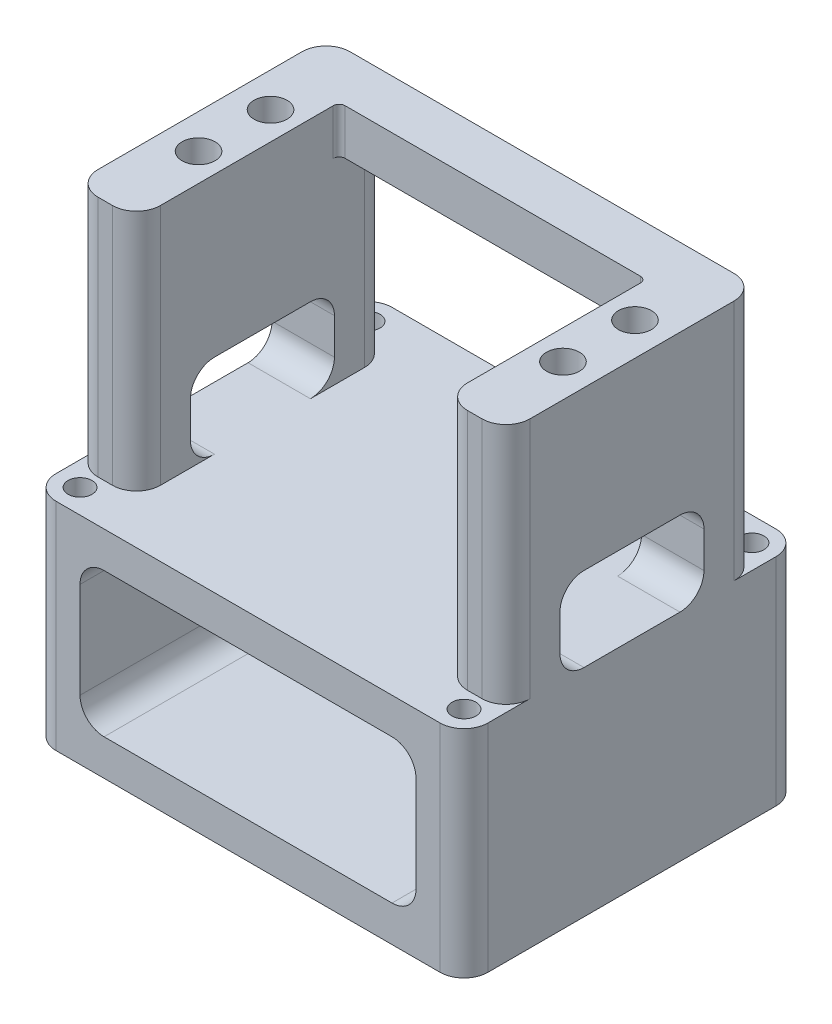
SolidWorks part; units mm, degrees
ref_plane "Front" through (0, 0, 0) normal (0, 0, 1) x (1, 0, 0)
ref_plane "Top" through (0, 0, 0) normal (0, 1, 0) x (1, 0, 0)
ref_plane "Right" through (0, 0, 0) normal (1, 0, 0) x (0, 0, -1)
sketch "Sketch1" plane through (0, 0, 0) normal (0, 0, 1) x (1, 0, 0)
  line L1 (28.575, -19.05) -> (-28.575, -19.05)
  line L2 (28.575, -19.05) -> (28.575, 19.05)
  line L3 (28.575, 19.05) -> (-28.575, 19.05)
  line L4 (-28.575, -19.05) -> (-28.575, 19.05)
  line L5 (28.575, -19.05) -> (-28.575, 19.05) construction
  line L6 (28.575, 19.05) -> (-28.575, -19.05) construction
  line L7 (-20.32, 13.0175) -> (20.32, 13.0175)
  line L8 (-20.32, 13.0175) -> (-20.32, -13.0175)
  line L9 (-20.32, -13.0175) -> (20.32, -13.0175)
  line L10 (20.32, 13.0175) -> (20.32, -13.0175)
  line L11 (-20.32, 13.0175) -> (20.32, -13.0175) construction
  line L12 (-20.32, -13.0175) -> (20.32, 13.0175) construction
  point P0 (0, 0)
  point P6 (0, 0)
  dimension "D1" = 57.15
  dimension "D2" = 38.1
  dimension "D3" = 26.035
  dimension "D4" = 40.64
extrude "Boss-Extrude1" add sketch "Sketch1" along normal mid plane 33.3375
sketch "Sketch3" plane through (0, 19.05, 0) normal (0, 1, 0) x (1, 0, 0)
  line L2 (20.32, -10.16) -> (20.32, 9.3663)
  line L3 (19.5263, 10.16) -> (-19.5263, 10.16)
  line L4 (-20.32, -10.16) -> (-20.32, 9.3662)
  line L5 (20.32, -10.16) -> (-20.32, 10.16) construction
  line L6 (20.32, 10.16) -> (-20.32, -10.16) construction
  line L8 (-20.32, -10.16) -> (-20.32, -16.6687)
  line L9 (-20.32, -16.6687) -> (20.32, -16.6687)
  line L10 (20.32, -16.6687) -> (20.32, -10.16)
  arc A0 (20.32, 9.3663) -> (19.5263, 10.16) centre (19.5263, 9.3663) ccw
  arc A3 (-19.5263, 10.16) -> (-20.32, 9.3662) centre (-19.5263, 9.3662) ccw
  point P0 (0, 0)
  dimension "D3" = 0.7937
  dimension "D1" = 40.64
  dimension "D2" = 20.32
extrude "Cut-Extrude1" cut sketch "Sketch3" against normal blind 30.9562
sketch "Sketch5" plane through (-28.575, 0, 0) normal (-1, 0, 0) x (0, 0, 1)
  line L0 (16.6687, -19.05) -> (-16.6687, -19.05) construction
  line L1 (-9.525, -1.905) -> (9.525, -1.905)
  line L2 (-9.525, -1.905) -> (-9.525, -13.0175)
  line L3 (-9.525, -13.0175) -> (9.525, -13.0175)
  line L4 (9.525, -1.905) -> (9.525, -13.0175)
  line L5 (-9.525, -1.905) -> (9.525, -13.0175) construction
  line L6 (-9.525, -13.0175) -> (9.525, -1.905) construction
  point P0 (0, -7.4613)
  dimension "D1" = 11.1125
  dimension "D2" = 19.05
  dimension "D3" = 6.0325
extrude "Cut-Extrude2" cut sketch "Sketch5" against normal up to surface (57.15 mm away) up to face at (28.575, 0, 0)
sketch "Sketch6" plane through (0, 19.05, 0) normal (0, 1, 0) x (1, 0, 0)
  line L3 (-32.2339, 0) -> (34.92, 0) construction
  line L4 (0, -27.9559) -> (0, 27.16) construction
  line L5 (-28.575, -16.6687) -> (-28.575, 16.6687) construction
  line L6 (28.575, -16.6687) -> (28.575, 16.6687) construction
  circle A0 centre (-24.0109, -4.7625) radius 2.1828
  circle A1 centre (-24.0109, 4.7625) radius 2.1828
  circle A2 centre (24.2094, -4.7625) radius 2.1828
  circle A3 centre (24.2094, 4.7625) radius 2.1828
  dimension "D3" = 4.7625
  dimension "D1" = 6.7469
  dimension "D2" = 4.3656
  dimension "D4" = 4.7625
  dimension "D5" = 4.3656
extrude "Cut-Extrude3" cut sketch "Sketch6" against normal blind 19.05
sketch "Sketch9" plane through (0, 0, 0) normal (0, 0, 1) x (1, 0, 0)
  line L0 (-28.575, 19.05) -> (-28.575, -19.05) construction
  line L1 (-28.575, -13.0175) -> (28.575, -13.0175)
  line L2 (-28.575, -13.0175) -> (-28.575, -41.5925)
  line L3 (-28.575, -41.5925) -> (28.575, -41.5925)
  line L4 (28.575, -13.0175) -> (28.575, -41.5925)
  line L5 (-20.32, -13.0175) -> (20.32, -13.0175) construction
  line L6 (28.575, -19.05) -> (28.575, 19.05) construction
  dimension "D1" = 28.575
extrude "Boss-Extrude2" add sketch "Sketch9" along normal mid plane 44.45
sketch "Sketch10" plane through (0, -13.0175, 0) normal (0, 1, 0) x (1, 0, 0)
  line L5 (28.575, 16.6687) -> (28.575, 22.225) construction
  line L16 (-28.575, 16.6687) -> (-28.575, 22.225) construction
  line L19 (28.575, 22.225) -> (-28.575, 22.225) construction
  line L21 (-36.0056, 0) -> (33.0665, 0) construction
  circle A0 centre (-25.4, 19.05) radius 1.5875
  circle A1 centre (25.4, 19.05) radius 1.5875
  circle A2 centre (-25.4, -19.05) radius 1.5875
  circle A3 centre (25.4, -19.05) radius 1.5875
  dimension "D3" = 3.175
  dimension "D4" = 3.175
  dimension "D5" = 1.5875
  dimension "D1" = 3.175
extrude "Cut-Extrude4" cut sketch "Sketch10" against normal up to surface (28.575 mm away) up to face at (0, -41.5925, 0)
sketch "Sketch11" plane through (0, -41.5925, 0) normal (0, -1, 0) x (1, 0, 0)
  line L0 (-28.575, 22.225) -> (28.575, 22.225) construction
  line L1 (19.05, -15.875) -> (-19.05, -15.875)
  line L2 (22.225, -12.7) -> (22.225, 12.7)
  line L3 (19.05, 15.875) -> (-19.05, 15.875)
  line L4 (-22.225, -12.7) -> (-22.225, 12.7)
  line L5 (22.225, -15.875) -> (-22.225, 15.875) construction
  line L6 (22.225, 15.875) -> (-22.225, -15.875) construction
  line L7 (-28.575, 22.225) -> (-28.575, -22.225) construction
  arc A0 (22.225, 12.7) -> (19.05, 15.875) centre (19.05, 12.7) ccw
  arc A1 (19.05, -15.875) -> (22.225, -12.7) centre (19.05, -12.7) ccw
  arc A2 (-19.05, -15.875) -> (-22.225, -12.7) centre (-19.05, -12.7) cw
  arc A3 (-19.05, 15.875) -> (-22.225, 12.7) centre (-19.05, 12.7) ccw
  point P0 (0, 0)
  dimension "D3" = 3.175
  dimension "D1" = 6.35
  dimension "D2" = 6.35
extrude "Cut-Extrude5" [suppressed] cut sketch "Sketch11" against normal blind 22.225
sketch "Sketch12" plane through (0, 0, 22.225) normal (0, 0, 1) x (1, 0, 0)
  line L1 (-22.225, -17.78) -> (22.225, -17.78)
  line L2 (-22.225, -17.78) -> (-22.225, -36.83)
  line L3 (-22.225, -36.83) -> (22.225, -36.83)
  line L4 (22.225, -17.78) -> (22.225, -36.83)
  line L6 (-23.8125, -27.305) -> (23.8125, -27.305) construction
  line L7 (-23.8125, -41.5925) -> (-23.8125, -13.0175) construction
  line L8 (23.8125, -13.0175) -> (23.8125, -41.5925) construction
  line L9 (0, -13.0175) -> (0, -41.5925) construction
  line L10 (28.575, -13.0175) -> (-28.575, -13.0175) construction
  line L11 (-28.575, -41.5925) -> (28.575, -41.5925) construction
  dimension "D1" = 19.05
  dimension "D3" = 44.45
extrude "Cut-Extrude6" cut sketch "Sketch12" against normal up to next
fillet "Fillet1" radius 3.175 24 edges at (-28.575, -27.305, -22.225) (28.575, -27.305, -22.225) (28.575, -27.305, 22.225) (-28.575, -27.305, 22.225) (20.32, 3.0163, 16.6687) (-20.32, 0, -16.6687) (20.32, 0, -16.6687) (28.575, 3.0163, 16.6687) (28.575, 3.0163, -16.6687) (-28.575, 3.0162, -16.6687) (-28.575, 3.0162, 16.6687) (-20.32, 3.0162, 16.6687) (24.4475, -1.905, 9.525) (24.4475, -13.0175, 9.525) (24.4475, -13.0175, -9.525) (24.4475, -1.905, -9.525) (-24.4475, -1.905, -9.525) (-24.4475, -1.905, 9.525) (-24.4475, -13.0175, 9.525) (-24.4475, -13.0175, -9.525) (-22.225, -36.83, 0) (22.225, -36.83, 0) (22.225, -17.78, 0) (-22.225, -17.78, 0)
